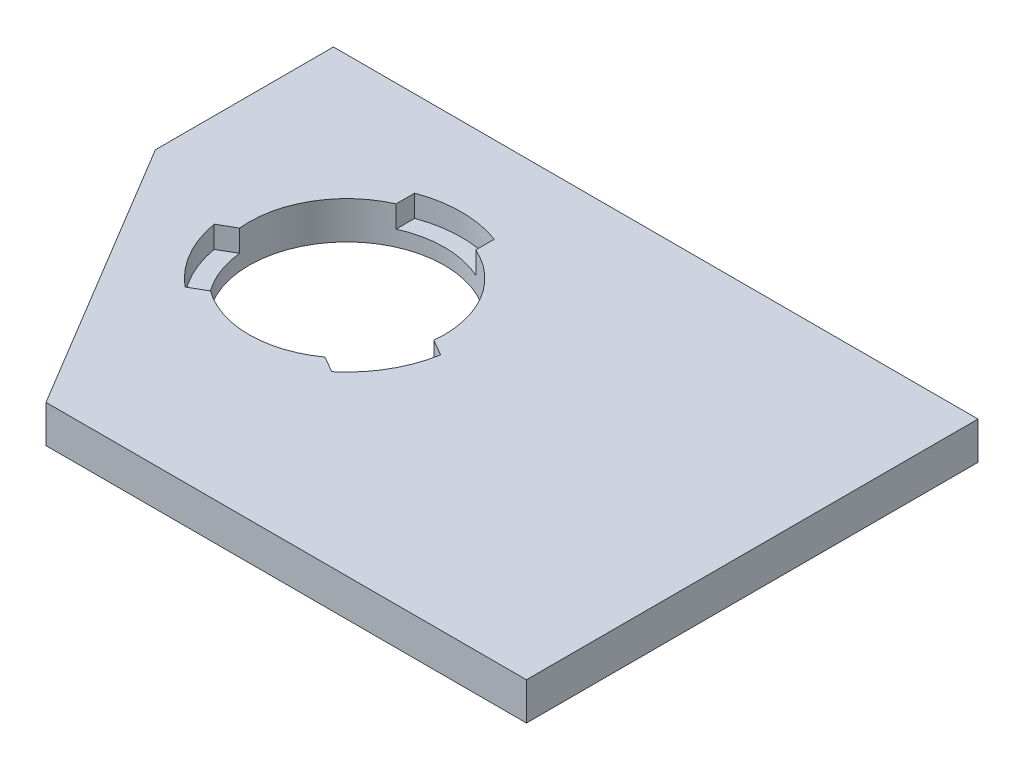
SolidWorks part; units mm, degrees
ref_plane "Front Plane" through (0, 0, 0) normal (0, 0, 1) x (1, 0, 0)
ref_plane "Top Plane" through (0, 0, 0) normal (0, 1, 0) x (1, 0, 0)
ref_plane "Right Plane" through (0, 0, 0) normal (1, 0, 0) x (0, 0, -1)
sketch "Sketch1" plane through (0, 0, 0) normal (0, 1, 0) x (1, 0, 0)
  line L1 (-20.3661, -10.164) -> (62.1339, -10.164)
  line L2 (-20.3661, -10.164) -> (-20.3661, 47.636)
  line L3 (-20.3661, 47.636) -> (62.1339, 47.636)
  line L4 (62.1339, -10.164) -> (62.1339, 47.636)
  dimension "D1" = 82.5
  dimension "D2" = 57.8
extrude "Boss-Extrude1" add sketch "Sketch1" along normal blind 4.8
sketch "Sketch2" plane through (0, 4.8, 0) normal (0, 1, 0) x (1, 0, 0)
  line L0 (41.1339, -10.164) -> (62.1339, 24.836)
  line L1 (-20.3661, -10.164) -> (62.1339, -10.164) construction
  line L2 (62.1339, -10.164) -> (62.1339, 47.636) construction
  line L3 (62.1339, 24.836) -> (62.1339, -10.164)
  line L4 (62.1339, -10.164) -> (41.1339, -10.164)
  circle A0 centre (35.6339, 22.836) radius 12.5
  dimension "D3" = 25
  dimension "D1" = 35
  dimension "D2" = 21
  dimension "D4" = 26.5
  dimension "D5" = 33
extrude "Cut-Extrude1" cut sketch "Sketch2" against normal blind 4.8
sketch "Sketch3" plane through (0, 4.8, 0) normal (0, 1, 0) x (1, 0, 0)
  line L0 (-20.3661, -10.164) -> (41.1339, -10.164) construction
  line L1 (62.1339, 24.836) -> (62.1339, 47.636) construction
  line L2 (35.6339, 22.836) -> (35.6339, 37.536)
  line L3 (35.6339, 22.836) -> (22.9033, 15.486)
  line L4 (35.6339, 22.836) -> (48.3645, 15.486)
  line L5 (35.6339, 37.536) -> (40.7339, 37.536)
  line L10 (40.7339, 37.536) -> (40.7339, 31.536)
  line L11 (40.7339, 31.536) -> (30.5339, 31.536)
  line L12 (30.5339, 31.536) -> (30.5339, 37.536)
  line L13 (30.5339, 37.536) -> (35.6339, 37.536)
  line L14 (48.3645, 15.486) -> (45.8145, 11.0693)
  line L15 (45.8145, 11.0693) -> (40.6183, 14.0693)
  line L16 (40.6183, 14.0693) -> (45.7183, 22.9027)
  line L17 (45.7183, 22.9027) -> (50.9145, 19.9027)
  line L18 (50.9145, 19.9027) -> (48.3645, 15.486)
  line L19 (22.9033, 15.486) -> (20.3533, 19.9027)
  line L20 (20.3533, 19.9027) -> (25.5495, 22.9027)
  line L21 (25.5495, 22.9027) -> (30.6495, 14.0693)
  line L22 (30.6495, 14.0693) -> (25.4533, 11.0693)
  line L23 (25.4533, 11.0693) -> (22.9033, 15.486)
  circle A0 centre (35.6339, 22.836) radius 14.7
  circle M23 centre (35.6339, 22.836) radius 12.5
  dimension "D1" = 29.4
  dimension "D2" = 33
  dimension "D3" = 26.5
  dimension "D4" = 120
  dimension "D5" = 120
  dimension "D6" = 5.1
  dimension "D7" = 5.1
  dimension "D8" = 6
  dimension "D9" = 3
extrude "Cut-Extrude2" cut sketch "Sketch3" against normal blind 2.8 contours L2 A0 L12 M23 | L10 A0 L2 M23 | L4 A0 L17 M23 | L15 A0 L4 M23 | L20 A0 L3 M23 | L3 A0 L22 M23
mirror "Mirror1" about plane through (62.1339, 4.8, 10.164) normal (-1, 0, 0) of "Boss-Extrude1", "Cut-Extrude1", "Cut-Extrude2"
sketch "Sketch4" plane through (0, 4.8, 0) normal (0, 1, 0) x (1, 0, 0)
  line L1 (-20.3661, 47.636) -> (62.1339, 47.636)
  line L2 (-20.3661, 47.636) -> (-20.3661, -10.164)
  line L3 (-20.3661, -10.164) -> (62.1339, -10.164)
  line L4 (62.1339, 47.636) -> (62.1339, -10.164)
  dimension "D1" = 57.8
  dimension "D2" = 82.5
extrude "Cut-Extrude3" cut sketch "Sketch4" against normal blind 10
